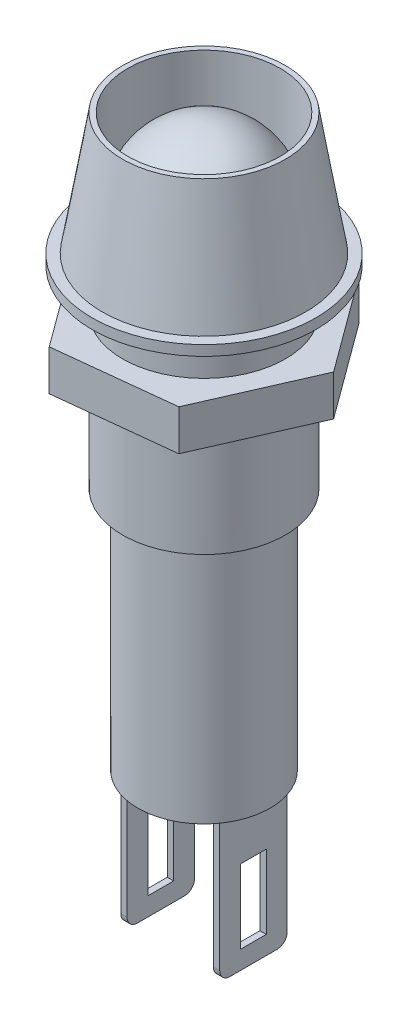
SolidWorks part; units mm, degrees
material "Stainless Steel 304"
ref_plane "Front Plane" through (0, 0, 0) normal (0, 0, 1) x (1, 0, 0)
ref_plane "Top Plane" through (0, 0, 0) normal (0, 1, 0) x (1, 0, 0)
ref_plane "Right Plane" through (0, 0, 0) normal (1, 0, 0) x (0, 0, -1)
sketch "Sketch1" plane through (0, 0, 0) normal (0, 0, 1) x (0, 1, 0)
  line L0 (0, 0) -> (-3.25, 0) construction
  line L1 (0, 0) -> (0, 3.25)
  line L2 (0, 3.25) -> (12, 3.25)
  line L3 (12, 3.25) -> (12, 4)
  line L4 (12, 4) -> (21.5, 4)
  line L5 (22, 5) -> (22, 5.5)
  line L6 (22, 5) -> (28, 4)
  line L7 (28, 4) -> (28, 3.75)
  line L8 (28, 3.75) -> (23, 3.75)
  line L9 (23, 3.75) -> (23, 3.5)
  line L10 (23, 3.5) -> (24, 3.5)
  line L11 (21.5, 4) -> (21.5, 5.5)
  line L12 (0, 0) -> (24, 0)
  line L13 (21.5, 5.5) -> (22, 5.5)
  line L14 (24, 3.5) -> (24, 0)
  arc A0 (27.5, 0) -> (24, 3.5) centre (24, 0) ccw construction
  dimension "D6" = 7
  dimension "D10" = 4
  dimension "D1" = 6.5
  dimension "D2" = 8
  dimension "D3" = 22
  dimension "D4" = 10
  dimension "D5" = 11
  dimension "D7" = 7.5
  dimension "D8" = 8
  dimension "D9" = 6
  dimension "D11" = 1
  dimension "D12" = 9.462
  dimension "D13" = 0.5
revolve "Revolve1" add sketch "Sketch1" angle 360 about L0
sketch "Sketch2" plane through (0, 0, 0) normal (0, -1, 0) x (1, 0, 0)
  line L0 (0, 0) -> (0, 3.25) construction
  line L1 (-2.4329, 1.6588) -> (-2.1196, 1.6588)
  line L2 (-2.4329, 1.6588) -> (-2.4329, -1.6588)
  line L3 (-2.4329, -1.6588) -> (-2.1196, -1.6588)
  line L4 (-2.1196, 1.6588) -> (-2.1196, -1.6588)
  line L5 (2.1196, 1.6588) -> (2.1196, -1.6588)
  line L6 (2.4329, -1.6588) -> (2.1196, -1.6588)
  line L7 (2.4329, 1.6588) -> (2.4329, -1.6588)
  line L8 (2.4329, 1.6588) -> (2.1196, 1.6588)
  circle A0 centre (0, 0) radius 3.25 construction
  point P10 (-2.1196, 0)
extrude "Boss-Extrude1" add sketch "Sketch2" along normal blind 7
sketch "Sketch3" plane through (-2.4329, 0, 0) normal (-1, 0, 0) x (0, 0, 1)
  line L1 (-0.6278, -2.4641) -> (0.6278, -2.4641)
  line L2 (-0.6278, -2.4641) -> (-0.6278, -6.0955)
  line L3 (-0.6278, -6.0955) -> (0.6278, -6.0955)
  line L4 (0.6278, -2.4641) -> (0.6278, -6.0955)
  point P4 (0, -2.4641)
extrude "Cut-Extrude1" cut sketch "Sketch3" against normal through all
fillet "Fillet1" radius 0.5 4 edges at (2.2762, -7, -1.6588) (2.2762, -7, 1.6588) (-2.2762, -7, -1.6588) (-2.2762, -7, 1.6588)
sketch "Sketch4" plane through (0, 21.5, 0) normal (0, -1, 0) x (1, 0, 0)
  line L1 (-2.3216, 5.2862) -> (-5.7388, 0.6325)
  line L2 (-5.7388, 0.6325) -> (-3.4171, -4.6537)
  line L3 (-3.4171, -4.6537) -> (2.3216, -5.2862)
  line L4 (2.3216, -5.2862) -> (5.7388, -0.6325)
  line L5 (5.7388, -0.6325) -> (3.4171, 4.6537)
  line L6 (3.4171, 4.6537) -> (-2.3216, 5.2862)
  circle A0 centre (0, 0) radius 5 construction
  dimension "D1" = 10
extrude "Boss-Extrude2" add sketch "Sketch4" along normal blind 2 from offset 2
sketch "Sketch5" plane through (0, 0, 0) normal (0, 0, 1) x (1, 0, 0)
  line L0 (-3.5, 24) -> (0, 24) construction
  line L1 (-3.5, 24) -> (0, 24)
  line L2 (0, 27.5) -> (0, 24)
  arc A0 (0, 27.5) -> (-3.5, 24) centre (0, 24) ccw construction
  arc A1 (0, 27.5) -> (-3.5, 24) centre (0, 24) ccw
revolve "Red" [suppressed] add sketch "Sketch5" angle 360 about L2
sketch "Sketch6" plane through (0, 0, 0) normal (0, 0, 1) x (1, 0, 0)
  line L2 (-3.5, 24) -> (0, 24)
  line L3 (0, 24) -> (0, 27.5)
  line L4 (-3.5, 24) -> (0, 24)
  line L5 (0, 24) -> (0, 27.5)
  arc A1 (0, 27.5) -> (-3.5, 24) centre (0, 24) ccw
  arc A2 (0, 27.5) -> (-3.5, 24) centre (0, 24) ccw
  dimension "D1" = 0
revolve "Green" add sketch "Sketch6" angle 360 about L5
